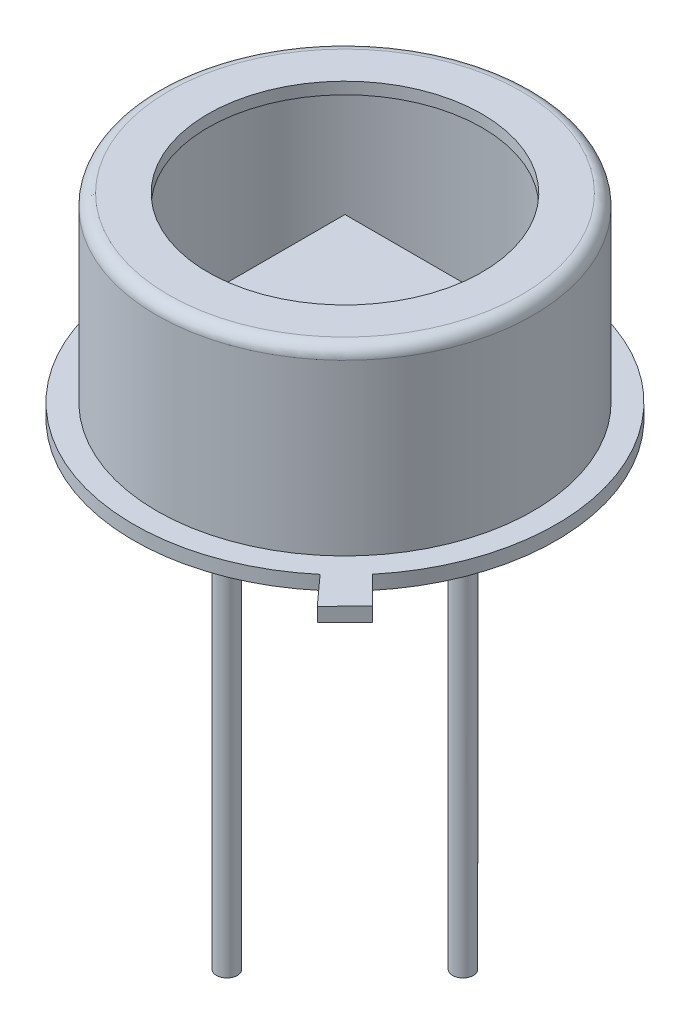
SolidWorks part; units mm, degrees
ref_plane "Front Plane" through (0, 0, 0) normal (0, 0, 1) x (1, 0, 0)
ref_plane "Top Plane" through (0, 0, 0) normal (0, 1, 0) x (1, 0, 0)
ref_plane "Right Plane" through (0, 0, 0) normal (1, 0, 0) x (0, 0, -1)
sketch "Sketch1" plane through (0, 0, 0) normal (0, 0, 1) x (1, 0, 0)
  line L0 (0, 0) -> (0, 37.7864) construction
  line L2 (4.55, 0) -> (4.55, 0.3)
  line L3 (4.55, 0.3) -> (4.05, 0.3)
  line L6 (4.05, 0.3) -> (4.05, 3.946)
  line L7 (3.796, 4.2) -> (2.95, 4.2)
  arc A0 (4.05, 3.946) -> (3.796, 4.2) centre (3.796, 3.946) ccw
  dimension "D7" = 0.254
  dimension "D1" = 0.3
  dimension "D2" = 8.1
  dimension "D4" = 9.1
  dimension "D6" = 4.2
  dimension "D8" = 5.9
revolve "Revolve-Thin2" add sketch "Sketch1" angle 360 about L0
sketch "Sketch2" plane through (0, 0, 0) normal (0, -1, 0) x (1, 0, 0)
  circle A1 centre (0, 0) radius 4.55
  circle A2 centre (0, 0) radius 4.55
  dimension "D1" = 0
extrude "Boss-Extrude1" add sketch "Sketch2" against normal up to surface (0.046 mm away) up to face at (0, 0.046, -3.796)
sketch "Sketch3" plane through (0, 0, 0) normal (0, -1, 0) x (1, 0, 0)
  line L0 (1.5, 1.5) -> (-1.5, -1.5) construction
  line L1 (-1.5, 1.5) -> (1.5, 1.5)
  line L2 (-1.5, 1.5) -> (-1.5, -1.5)
  line L3 (-1.5, -1.5) -> (1.5, -1.5)
  line L4 (1.5, 1.5) -> (1.5, -1.5)
  dimension "D1" = 3
extrude "Boss-Extrude2" add sketch "Sketch3" along normal blind 0.508 from offset 2.3 separate body offset against normal yes
sketch "Sketch4" plane through (0, 0, 0) normal (0, -1, 0) x (1, 0, 0)
  line L0 (-4.55, 0) -> (0, 0) construction
  line L5 (0, 0) -> (3.8001, 3.8001) construction
  line L6 (0, 0) -> (4.5545, 0) construction
  line L7 (3.4992, 2.9083) -> (2.9389, 3.4736)
  line L8 (3.4992, 2.9083) -> (4.0968, 3.5008)
  line L9 (4.0968, 3.5008) -> (3.5034, 4.0995)
  line L11 (3.5034, 4.0995) -> (2.9389, 3.4736)
  circle A0 centre (0, 0) radius 4.55 construction
  point P6 (-4.55, 0)
  dimension "D1" = 2.9389
  dimension "D2" = 3.5034
  dimension "D3" = 45
extrude "Boss-Extrude3" add sketch "Sketch4" against normal up to surface (0.3 mm away) up to face at (0, 0.3, -4.05)
sketch "Sketch5" plane through (0, 0, 0) normal (0, -1, 0) x (1, 0, 0)
  line L0 (0, 0) -> (0, 2.54) construction
  line L2 (-2.54, 0) -> (2.54, 0) construction
  circle A0 centre (0, 0) radius 2.54 construction
  circle A1 centre (-2.54, 0) radius 0.225
  circle A2 centre (2.54, 0) radius 0.225
  circle A3 centre (0, 2.54) radius 0.225
  dimension "D1" = 5.08
  dimension "D2" = 0.45
  dimension "D3" = 5.08
  dimension "D4" = 0.45
  dimension "D5" = 0.45
extrude "Boss-Extrude4" add sketch "Sketch5" along normal blind 9
sketch "Sketch7" plane through (0, 0, 0) normal (0, -1, 0) x (1, 0, 0)
  circle A0 centre (0, 2.54) radius 0.75
  dimension "D1" = 1.5
extrude "Boss-Extrude5" add sketch "Sketch7" along normal blind 0.4
